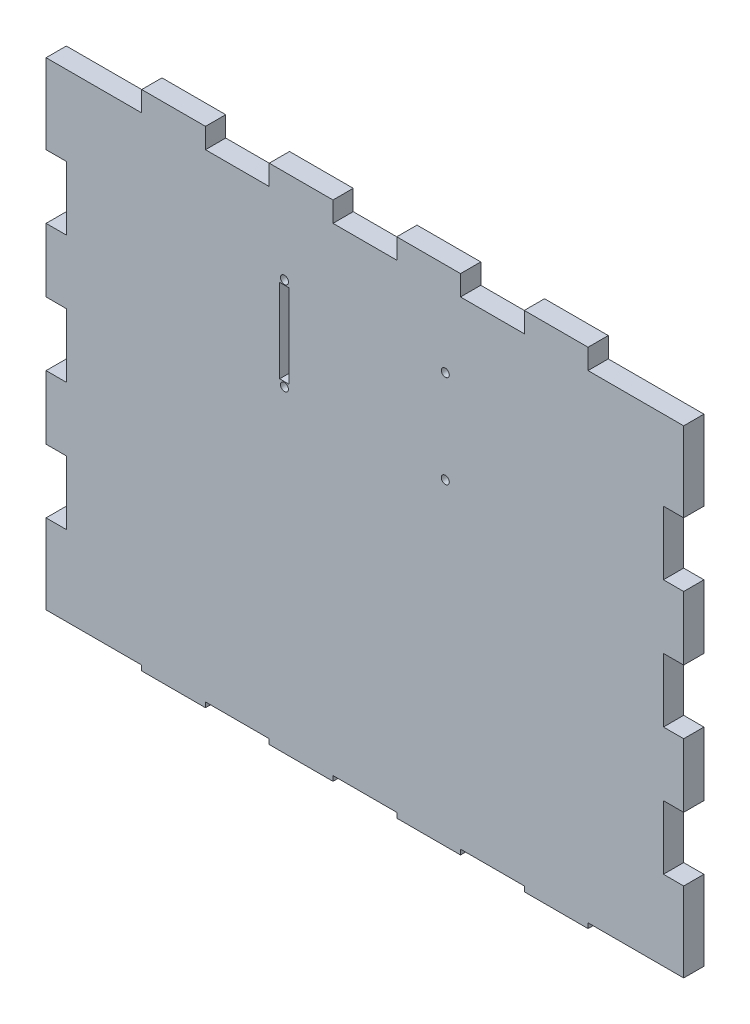
SolidWorks part; units mm, degrees
ref_plane "Front Plane" through (0, 0, 0) normal (0, 0, 1) x (1, 0, 0)
ref_plane "Top Plane" through (0, 0, 0) normal (0, 1, 0) x (1, 0, 0)
ref_plane "Right Plane" through (0, 0, 0) normal (1, 0, 0) x (0, 0, -1)
sketch "Sketch1" plane through (0, 0, 0) normal (0, 0, 1) x (1, 0, 0)
  line L0 (0, 75) -> (200, 75) construction
  line L1 (0, 0) -> (200, 0)
  line L2 (0, 0) -> (0, 150)
  line L3 (0, 150) -> (200, 150)
  line L4 (200, 0) -> (200, 150)
  line L5 (100, 0) -> (100, 150) construction
  line L6 (70, 0) -> (70, -1.5875)
  line L7 (30, 0) -> (50, 0)
  line L8 (30, 0) -> (30, -1.5875)
  line L9 (30, -1.5875) -> (50, -1.5875)
  line L10 (50, 0) -> (50, -1.5875)
  line L11 (70, 0) -> (90, 0)
  line L12 (90, 0) -> (90, -1.5875)
  line L13 (70, -1.5875) -> (90, -1.5875)
  line L14 (110, 0) -> (110, -1.5875)
  line L15 (110, 0) -> (130, 0)
  line L16 (130, 0) -> (130, -1.5875)
  line L17 (110, -1.5875) -> (130, -1.5875)
  line L18 (150, 0) -> (150, -1.5875)
  line L19 (150, 0) -> (170, 0)
  line L20 (170, 0) -> (170, -1.5875)
  line L21 (150, -1.5875) -> (170, -1.5875)
  line L22 (70, 150) -> (70, 156.35)
  line L23 (30, 150) -> (50, 150)
  line L24 (30, 150) -> (30, 156.35)
  line L25 (30, 156.35) -> (50, 156.35)
  line L26 (50, 150) -> (50, 156.35)
  line L27 (70, 150) -> (90, 150)
  line L28 (90, 150) -> (90, 156.35)
  line L29 (70, 156.35) -> (90, 156.35)
  line L30 (110, 150) -> (110, 156.35)
  line L31 (110, 150) -> (130, 150)
  line L32 (130, 150) -> (130, 156.35)
  line L33 (110, 156.35) -> (130, 156.35)
  line L34 (150, 150) -> (150, 156.35)
  line L35 (150, 150) -> (170, 150)
  line L36 (170, 150) -> (170, 156.35)
  line L37 (150, 156.35) -> (170, 156.35)
  line L38 (0, 85) -> (0, 65)
  line L39 (0, 125) -> (6.35, 125)
  line L40 (0, 125) -> (0, 105)
  line L41 (0, 105) -> (6.35, 105)
  line L42 (6.35, 125) -> (6.35, 105)
  line L43 (0, 85) -> (6.35, 85)
  line L44 (6.35, 85) -> (6.35, 65)
  line L45 (0, 65) -> (6.35, 65)
  line L46 (0, 45) -> (0, 25)
  line L47 (0, 45) -> (6.35, 45)
  line L48 (6.35, 45) -> (6.35, 25)
  line L49 (0, 25) -> (6.35, 25)
  line L50 (200, 45) -> (193.65, 45)
  line L51 (193.65, 45) -> (193.65, 25)
  line L52 (200, 25) -> (193.65, 25)
  line L53 (200, 45) -> (200, 25)
  line L54 (200, 85) -> (193.65, 85)
  line L55 (193.65, 85) -> (193.65, 65)
  line L56 (200, 65) -> (193.65, 65)
  line L57 (200, 85) -> (200, 65)
  line L58 (200, 105) -> (193.65, 105)
  line L59 (193.65, 125) -> (193.65, 105)
  line L60 (200, 125) -> (193.65, 125)
  line L61 (200, 125) -> (200, 105)
  line L62 (100, 127.05) -> (100, 97.95) construction
  line L63 (74.7698, 127.05) -> (125.2302, 127.05) construction
  line L64 (74.7698, 127.05) -> (74.7698, 97.95) construction
  line L65 (74.7698, 97.95) -> (125.2302, 97.95) construction
  line L66 (125.2302, 127.05) -> (125.2302, 97.95) construction
  line L67 (74.7698, 112.5) -> (125.2302, 112.5) construction
  line L68 (74.7698, 125.6) -> (74.7698, 99.4) construction
  line L69 (73.2698, 125.6) -> (76.2698, 125.6)
  line L70 (73.2698, 125.6) -> (73.2698, 99.4)
  line L71 (73.2698, 99.4) -> (76.2698, 99.4)
  line L72 (76.2698, 125.6) -> (76.2698, 99.4)
  circle A0 centre (74.7698, 127.05) radius 1.25
  circle A2 centre (125.2302, 127.05) radius 1.25
  circle A3 centre (125.2302, 97.95) radius 1.25
  circle A4 centre (74.7698, 97.95) radius 1.25
  dimension "D21" = 2.5
  dimension "D1" = 200
  dimension "D2" = 150
  dimension "D3" = 20
  dimension "D4" = 1.5875
  dimension "D6" = 20
  dimension "D7" = 10
  dimension "D8" = 6.35
  dimension "D9" = 20
  dimension "D11" = 20
  dimension "D12" = 10
  dimension "D13" = 6.35
  dimension "D14" = 20
  dimension "D16" = 20
  dimension "D17" = 10
  dimension "D18" = 58.25
  dimension "D19" = 29.1
  dimension "D20" = 37.5
  dimension "D22" = 3
  dimension "D23" = 13.1
  dimension "D24" = 13.1
  dimension "D5" = 4
  dimension "D10" = 4
  dimension "D15" = 3
extrude "Boss-Extrude4" add sketch "Sketch1" along normal blind 6.35 contours L60 L4 L3 L2 L39 L42 L41 L43 L44 L45 L47 L48 L49 L1 L52 L51 L50 L56 L55 L54 L58 L59 A2 A0 L69 L72 | L8 L7 L10 L9 | L6 L13 L12 L11 | L14 L17 L16 L15 | L18 L21 L20 L19 | L34 L37 L36 L35 | L30 L33 L32 L31 | L22 L29 L28 L27 | L24 L23 L26 L25
